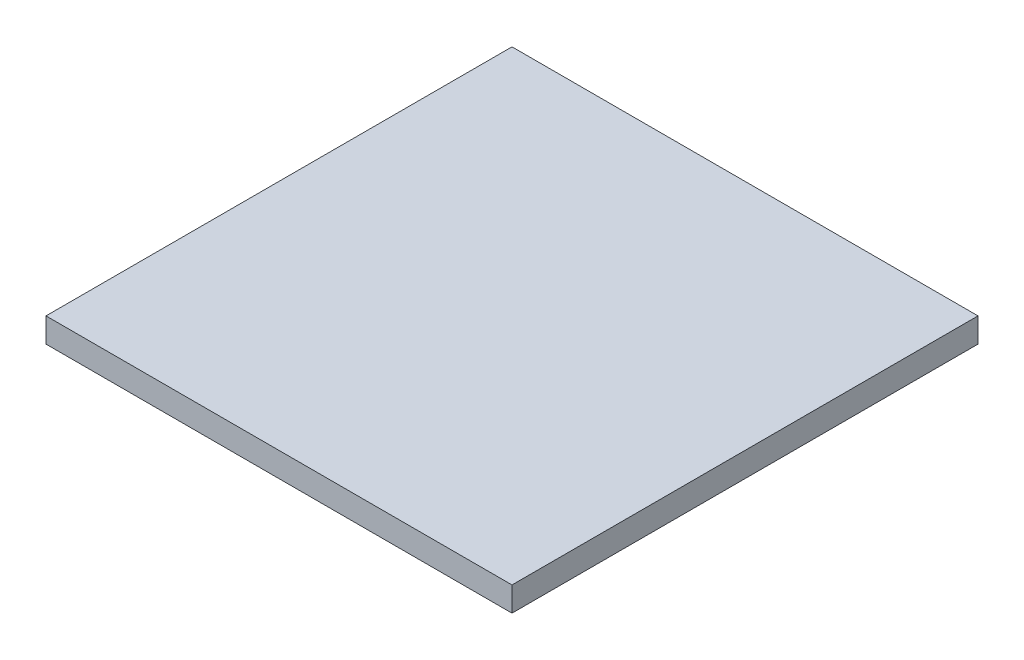
SolidWorks part; units mm, degrees
material "Silicon"
ref_plane "Plan de face" through (0, 0, 0) normal (0, 0, 1) x (1, 0, 0)
ref_plane "Plan de dessus" through (0, 0, 0) normal (0, 1, 0) x (1, 0, 0)
ref_plane "Plan de droite" through (0, 0, 0) normal (1, 0, 0) x (0, 0, -1)
sketch "Sketch2" plane through (0, 0, 0) normal (0, 1, 0) x (1, 0, 0)
  line L1 (-5, 5) -> (5, 5)
  line L2 (-5, 5) -> (-5, -5)
  line L3 (-5, -5) -> (5, -5)
  line L4 (5, 5) -> (5, -5)
  point P4 (0, 5)
  point P6 (-5, 0)
  dimension "D1" = 10
  dimension "D2" = 10
extrude "Boss-Extrude1" add sketch "Sketch2" along normal blind 0.525
equation "\"0.5.00mm\"=10"
